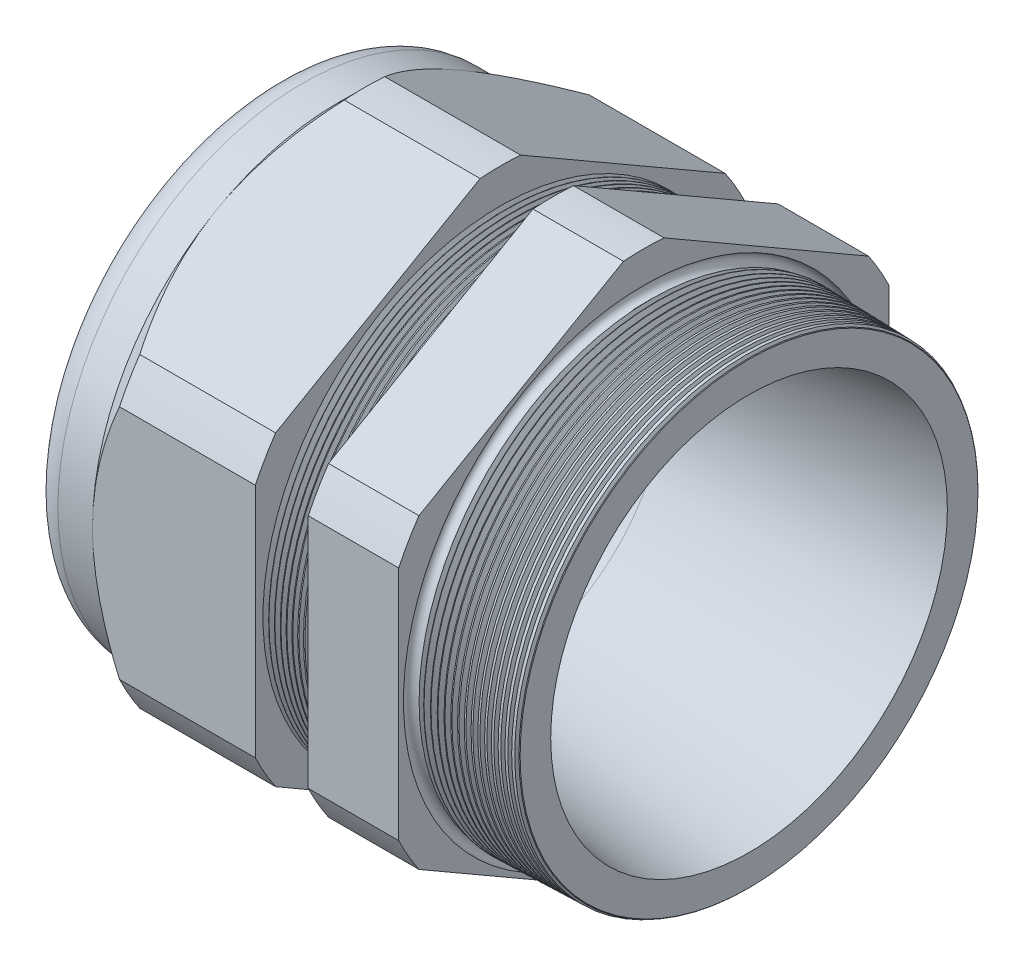
SolidWorks part; units mm, degrees
ref_plane "Front Plane" through (0, 0, 0) normal (0, 0, 1) x (1, 0, 0)
ref_plane "Top Plane" through (0, 0, 0) normal (0, 1, 0) x (1, 0, 0)
ref_plane "Right Plane" through (0, 0, 0) normal (1, 0, 0) x (0, 0, -1)
sketch "Sketch10" plane through (0, 0, 0) normal (0, 0, 1) x (1, 0, 0)
  line L0 (0, 0) -> (-115.3565, 0) construction
  line L1 (-56.896, 21.971) -> (-26.8936, 21.971)
  line L2 (6.096, 26.3141) -> (6.096, 30.6321)
  line L3 (-7.874, 30.998) -> (6.096, 30.6321)
  line L4 (-7.874, 65.024) -> (-7.874, 30.998)
  line L5 (-7.874, 65.024) -> (-19.874, 65.024)
  line L6 (-19.874, 65.024) -> (-19.874, 31.3122)
  line L7 (-26.8936, 31.496) -> (-19.874, 31.3122)
  line L8 (-26.8936, 31.496) -> (-26.8936, 65.024)
  line L9 (-26.8936, 65.024) -> (-48.496, 65.024)
  line L10 (-48.496, 65.024) -> (-48.496, 32.512)
  line L11 (-48.496, 32.512) -> (-56.896, 32.512)
  line L12 (-56.896, 32.512) -> (-56.896, 21.971)
  line L13 (-26.8936, 21.971) -> (6.096, 26.3141)
  dimension "D1" = 62.992
  dimension "D2" = 43.942
  dimension "D3" = 1.5
  dimension "D4" = 4.318
  dimension "A" = 62.992
  dimension "D6" = 65.024
  dimension "D8" = 130.048
  dimension "D9" = 8.4
  dimension "D10" = 21.6024
  dimension "D11" = 12
  dimension "D" = 13.97
revolve "Revolve2" add sketch "Sketch10" angle 360 about L0
sketch "Sketch12" plane through (-48.496, 0, 0) normal (-1, 0, 0) x (0, 0, 1)
  line L1 (-2.6912, 35.9878) -> (-29.8208, 20.3246)
  line L2 (-32.512, 15.6632) -> (-32.512, -15.6632)
  line L3 (-29.8208, -20.3246) -> (-2.6912, -35.9878)
  line L4 (2.6912, -35.9878) -> (29.8208, -20.3246)
  line L5 (32.512, -15.6632) -> (32.512, 15.6632)
  line L6 (29.8208, 20.3246) -> (2.6912, 35.9878)
  circle A0 centre (0, 0) radius 32.512 construction
  arc A1 (2.6912, 35.9878) -> (-2.6912, 35.9878) centre (0, 0) ccw
  arc A2 (-29.8208, 20.3246) -> (-32.512, 15.6632) centre (0, 0) ccw
  arc A3 (-32.512, -15.6632) -> (-29.8208, -20.3246) centre (0, 0) ccw
  arc A4 (-2.6912, -35.9878) -> (2.6912, -35.9878) centre (0, 0) ccw
  arc A5 (29.8208, -20.3246) -> (32.512, -15.6632) centre (0, 0) ccw
  arc A6 (32.512, 15.6632) -> (29.8208, 20.3246) centre (0, 0) ccw
  dimension "D2" = 72.1766
  dimension "D1" = 65.024
extrude "Cut-Extrude2" cut sketch "Sketch12" against normal through all flip side to cut
fillet "Fillet4" radius 3.81 1 edges at (-56.896, 0, -32.512)
sketch "Sketch19" plane through (-48.496, 0, 0) normal (-1, 0, 0) x (0, 0, 1)
  line L0 (32.512, 0) -> (32.512, 15.6632) construction
  circle A0 centre (0, 0) radius 32.512
extrude "Cut-Extrude3" cut sketch "Sketch19" against normal blind 3.998 draft 45 flip side to cut
chamfer "Chamfer1" distance 0.254 angle 45 1 edges at (6.096, 0, -30.6321)
sketch "Sketch21" plane through (-56.896, 0, 0) normal (-1, 0, 0) x (0, 0, 1)
  circle A0 centre (0, 0) radius 21.971
  circle A2 centre (0, 0) radius 21.971 construction
extrude "plug" add sketch "Sketch21" against normal blind 12.7 separate body
sketch "Sketch22" plane through (-56.896, 0, 0) normal (-1, 0, 0) x (0, 0, 1)
  circle A0 centre (0, 0) radius 21.717
  circle A1 centre (0, 0) radius 21.971 construction
  dimension "D1" = 0.254
extrude "Cut-Extrude4" cut sketch "Sketch22" against normal blind 0.508
sketch "Sketch27" plane through (-56.388, 0, 0) normal (-1, 0, 0) x (0, 0, 1)
  line L0 (-4.3624, 0) -> (4.3624, 0) construction
  circle A0 centre (-16.7442, 0) radius 4.953
  circle A1 centre (0, 0) radius 21.717 construction
  dimension "D1" = 0.0198
  dimension "holedia" = 9.906
extrude "plugholes" cut sketch "Sketch27" against normal through all
pattern_circular "CirPattern1" count 8 over 360 about axis through (0, 0, 0) along (1, 0, 0) of "plugholes"
sketch "Sketch28" [suppressed] plane through (-38.354, 0, 0) normal (-1, 0, 0) x (0, 0, 1)
  circle A0 centre (0, 0) radius 1.905
  dimension "midholedia" = 9.906
extrude "midhole" [suppressed] cut sketch "Sketch28" against normal through all
sketch "Sketch29" plane through (0, 0, 0) normal (0, 0, 1) x (1, 0, 0)
  line L0 (-26.8936, 31.496) -> (-26.1606, 31.4768)
  line L1 (-19.874, 31.3122) -> (-26.8936, 31.496) construction
  line L2 (-26.1606, 31.4768) -> (-26.5437, 30.8516)
  line L3 (-26.5437, 30.8516) -> (-26.8936, 31.496)
  dimension "D1" = 60
  dimension "D2" = 60
  dimension "D3" = 0.635
revolve "Cut-Revolve1" cut sketch "Sketch29" angle 360 about axis through (0, 0, 0) along (-1, 0, 0)
pattern_linear "LPattern1" count 9 spacing 0.762 along (1, 0, 0) of "Cut-Revolve1"
sketch "Sketch30" plane through (0, 0, 0) normal (0, 0, 1) x (1, 0, 0)
  line L0 (-7.874, 30.998) -> (-6.9944, 30.9749)
  line L1 (-7.874, 35.9878) -> (-7.874, 20.3246) construction
  line L2 (5.8421, 30.6388) -> (-7.874, 30.998) construction
  line L3 (-6.9944, 30.9749) -> (-7.4542, 30.2247)
  line L4 (-7.4542, 30.2247) -> (-7.874, 30.998)
  dimension "D1" = 60
  dimension "D2" = 60
  dimension "D3" = 0.762
revolve "Cut-Revolve2" cut sketch "Sketch30" angle 360 about axis through (0, 0, 0) along (-1, 0, 0)
pattern_linear "LPattern2" count 16 spacing 0.889 along (1, 0, 0) of "Cut-Revolve2"
sketch "Sketch31" [suppressed] plane through (-38.354, 0, 0) normal (-1, 0, 0) x (0, 0, 1)
  line L0 (-1.905, 1.905) -> (1.905, 1.905)
  line L1 (-1.905, -1.905) -> (1.905, -1.905)
  circle A0 centre (0, 0) radius 1.905 construction
  arc A1 (-1.905, 1.905) -> (-1.905, -1.905) centre (-1.905, 0) ccw
  arc A2 (1.905, 1.905) -> (1.905, -1.905) centre (1.905, 0) cw
extrude "Cut-Extrude5" [suppressed] cut sketch "Sketch31" against normal through all
sketch "Sketch32" plane through (0, 0, 0) normal (0, 0, 1) x (1, 0, 0)
  line L0 (-7.874, 35.9878) -> (-7.874, 20.3246) construction
  circle A0 centre (-7.747, 30.998) radius 0.889
  dimension "D2" = 1.778
  dimension "D1" = 0.127
revolve "Cut-Revolve3" cut sketch "Sketch32" angle 360 about axis through (0, 0, 0) along (-1, 0, 0)
